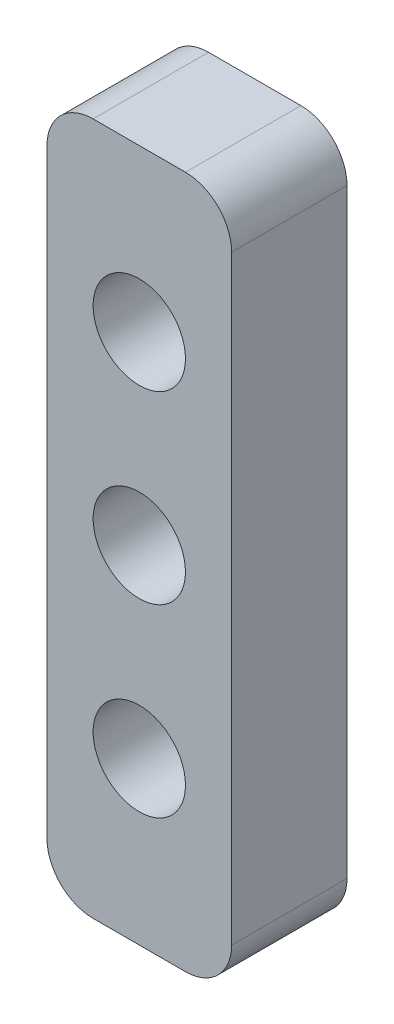
SolidWorks part; units mm, degrees
ref_plane "Front Plane" through (0, 0, 0) normal (0, 0, 1) x (1, 0, 0)
ref_plane "Top Plane" through (0, 0, 0) normal (0, 1, 0) x (1, 0, 0)
ref_plane "Right Plane" through (0, 0, 0) normal (1, 0, 0) x (0, 0, -1)
sketch "Sketch1" plane through (0, 0, 0) normal (0, 0, 1) x (1, 0, 0)
  line L0 (0, -13) -> (0, 13)
  line L1 (8, -13) -> (8, 13)
  line L2 (2, 15) -> (6, 15)
  line L3 (2, -15) -> (6, -15)
  line L4 (8, -14.5) -> (8, 14.5) construction
  line L5 (0, -14.5) -> (0, 14.5) construction
  arc A0 (8, 13) -> (6, 15) centre (6, 13) ccw
  arc A1 (0, 13) -> (2, 15) centre (2, 13) cw
  arc A2 (0, -13) -> (2, -15) centre (2, -13) ccw
  arc A3 (8, -13) -> (6, -15) centre (6, -13) cw
  point P4 (0, 0)
  point P13 (0, 15)
  dimension "D3" = 2
  dimension "D1" = 30
  dimension "D2" = 8
extrude "Boss-Extrude1" add sketch "Sketch1" along normal blind 5
sketch "Sketch3" plane through (0, 0, 5) normal (0, 0, 1) x (1, 0, 0)
  line L0 (0, 0) -> (10.5795, 0) construction
  line L1 (4, 15) -> (4, -16.6132) construction
  line L2 (6, 15) -> (2, 15) construction
  circle A0 centre (4, 0) radius 2
  circle A1 centre (4, 8) radius 2
  circle A2 centre (4, -8) radius 2
  dimension "D1" = 4
  dimension "D2" = 4
  dimension "D3" = 4
  dimension "D4" = 8
  dimension "D5" = 8
extrude "Cut-Extrude2" cut sketch "Sketch3" against normal through all
